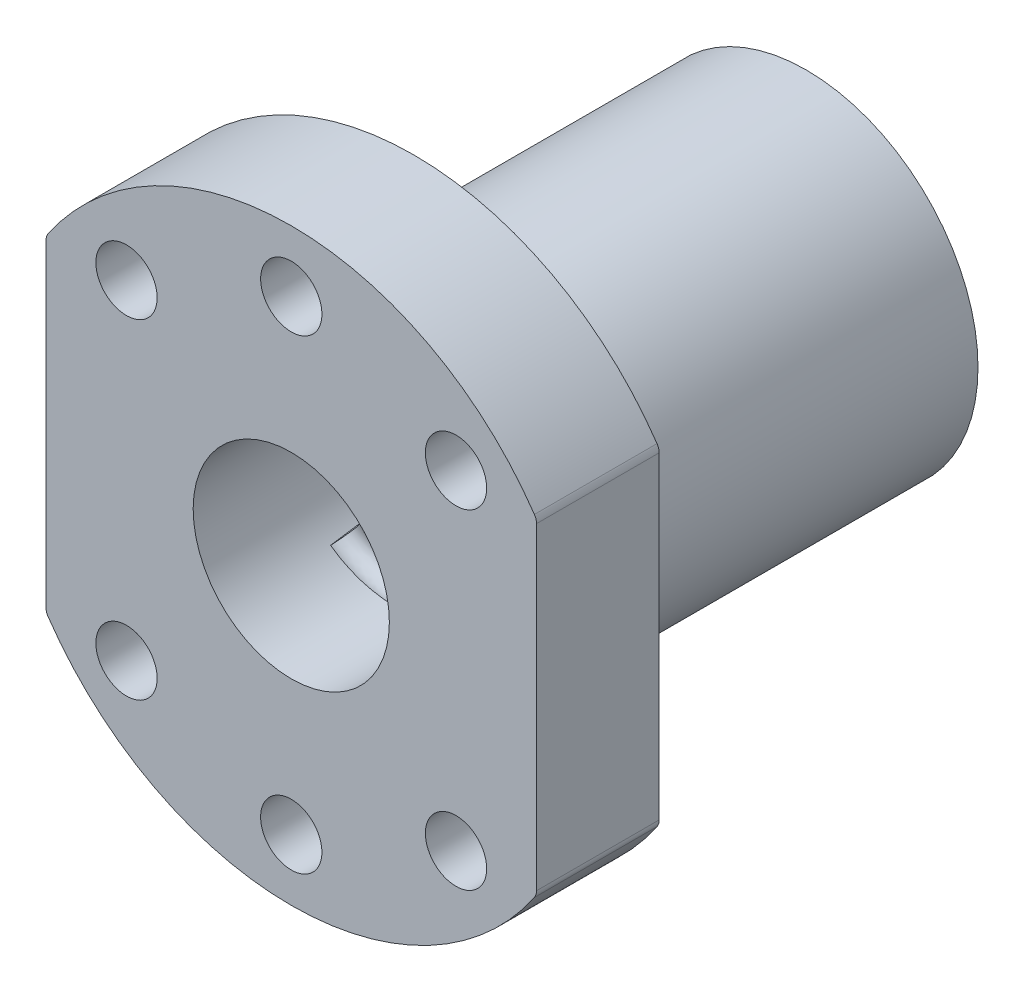
SolidWorks part; units mm, degrees
ref_plane "Front Plane" through (0, 0, 0) normal (0, 0, 1) x (1, 0, 0)
ref_plane "Top Plane" through (0, 0, 0) normal (0, 1, 0) x (1, 0, 0)
ref_plane "Right Plane" through (0, 0, 0) normal (1, 0, 0) x (0, 0, -1)
sketch "Sketch1" plane through (0, 0, 0) normal (0, 0, 1) x (1, 0, 0)
  line L0 (0, 0) -> (0, 19.677) construction
  line L1 (0, 0) -> (0, -22.9456) construction
  line L2 (-30.9863, 0) -> (0, 0) construction
  line L3 (0, 0) -> (30.7902, 0) construction
  line L4 (0, 0) -> (-13.435, -13.435) construction
  line L5 (0, 0) -> (13.435, -13.435) construction
  line L6 (0, 0) -> (-20, 0) construction
  line L7 (-20, 13.2665) -> (-20, 0)
  line L8 (-20, 0) -> (-20, -13.2665)
  line L9 (20, 0) -> (20, -13.2665)
  line L10 (20, 13.2665) -> (20, 0)
  circle A0 centre (0, 0) radius 8
  circle A1 centre (0, 0) radius 19 construction
  arc A2 (-20, -13.2665) -> (20, -13.2665) centre (0, 0) ccw
  circle A3 centre (-13.435, -13.435) radius 2.5
  circle A4 centre (0, -19) radius 2.5
  circle A5 centre (13.435, -13.435) radius 2.5
  circle A6 centre (13.435, 13.435) radius 2.5
  circle A7 centre (0, 19) radius 2.5
  circle A8 centre (-13.435, 13.435) radius 2.5
  arc A9 (20, 13.2665) -> (-20, 13.2665) centre (0, 0) ccw
  dimension "D1" = 16
  dimension "D2" = 38
  dimension "D3" = 48
  dimension "D6" = 5
  dimension "D7" = 5
  dimension "D8" = 5
  dimension "D4" = 45
  dimension "D5" = 45
  dimension "D9" = 20
extrude "Boss-Extrude1" add sketch "Sketch1" against normal blind 10
sketch "Sketch2" plane through (0, 0, -10) normal (0, 0, -1) x (-1, 0, 0)
  circle A0 centre (0, 0) radius 14
  circle A1 centre (0, 0) radius 8
  dimension "D1" = 28
  dimension "D2" = 16
extrude "Boss-Extrude2" add sketch "Sketch2" along normal blind 32
ref_plane "Plane1" through (0, 0, -10) normal (0, 0, 1) x (1, 0, 0)
sketch "Sketch4" plane through (0, 0, -10) normal (0, 0, 1) x (1, 0, 0)
  circle A0 centre (0, 0) radius 8 construction
  circle A1 centre (0, 0) radius 8
curve "Helix/Spiral1" pitch 5 height 25 turns 5
ref_plane "Plane2" through (-5.6569, -5.6569, -10) normal (0.7036, -0.7036, -0.099) x (-0.07, 0.07, -0.9951)
sketch "Sketch5" plane through (-5.6569, -5.6569, -10) normal (0.7036, -0.7036, -0.099) x (-0.07, 0.07, -0.9951)
  line L0 (-0.0157, 0.0052) -> (-0.0157, 5.2174) construction
  line L1 (-0.0157, 0.0052) -> (4.5173, 0.0052) construction
  line L2 (-0.0157, 0.0052) -> (-0.0157, -4.58) construction
  line L3 (-0.0157, 0.0052) -> (-4.8359, 0.0052) construction
  circle A0 centre (-0.0157, -0.2948) radius 1.25
  dimension "D2" = 2.5
  dimension "D1" = 0.3
sweep "Sweep1" add profiles "Sketch5" path "Helix/Spiral1"
fillet "Fillet1" radius 1 4 edges at (-20, 13.2665, -5) (-20, -13.2665, -5) (20, -13.2665, -5) (20, 13.2665, -5)
